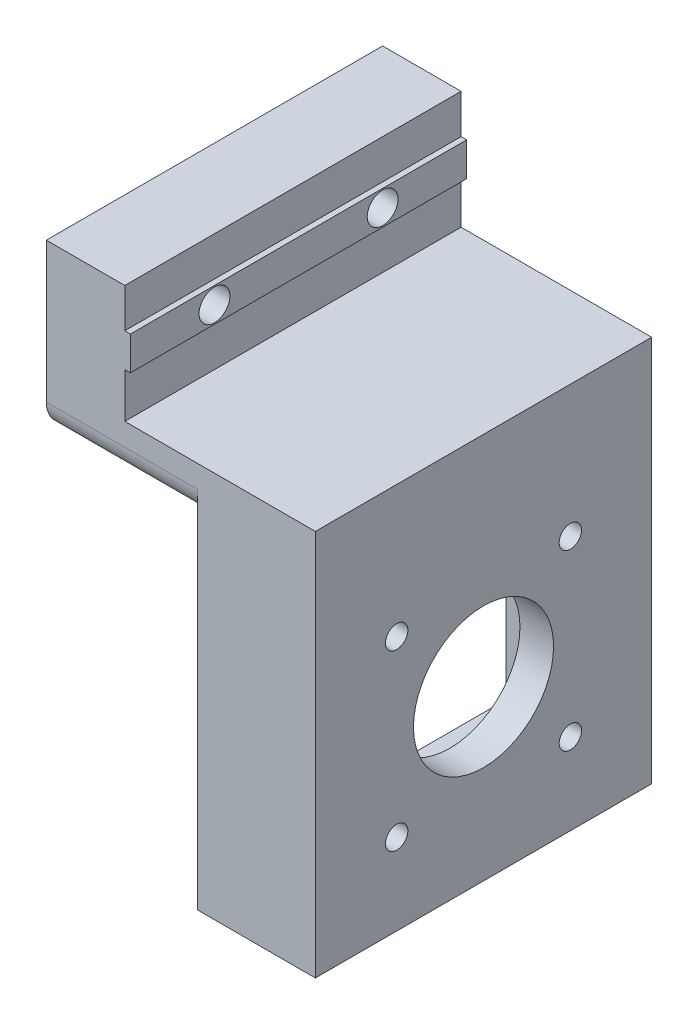
SolidWorks part; units mm, degrees
ref_plane "Alzado" through (0, 0, 0) normal (0, 0, 1) x (1, 0, 0)
ref_plane "Planta" through (0, 0, 0) normal (0, 1, 0) x (1, 0, 0)
ref_plane "Vista lateral" through (0, 0, 0) normal (1, 0, 0) x (0, 0, -1)
sketch "Croquis1" plane through (0, 0, 0) normal (0, 0, 1) x (1, 0, 0)
  line L0 (0, 0) -> (0, -30)
  line L1 (0, -30) -> (42, -30)
  line L2 (42, -30) -> (42, -90)
  line L3 (42, -90) -> (48, -90)
  line L4 (48, -90) -> (48, -21)
  line L5 (48, -21) -> (14, -21)
  line L6 (14, -21) -> (14, 0)
  line L7 (14, 0) -> (0, 0)
  dimension "D1" = 14
  dimension "D2" = 30
  dimension "D3" = 34
  dimension "D4" = 21
  dimension "D5" = 6
  dimension "D6" = 60
extrude "Saliente-Extruir1" add sketch "Croquis1" along normal blind 60
sketch "Croquis2" plane through (48, 0, 0) normal (1, 0, 0) x (0, 0, -1)
  line L0 (0, -90) -> (0, -21) construction
  line L1 (-45.5, -44.5) -> (-14.5, -44.5) construction
  line L2 (-45.5, -44.5) -> (-45.5, -75.5) construction
  line L3 (-45.5, -75.5) -> (-14.5, -75.5) construction
  line L4 (-14.5, -44.5) -> (-14.5, -75.5) construction
  line L5 (-60, -90) -> (0, -90) construction
  line L6 (-45.5, -44.5) -> (-14.5, -75.5) construction
  circle A0 centre (-45.5, -44.5) radius 2
  circle A1 centre (-14.5, -44.5) radius 2
  circle A2 centre (-45.5, -75.5) radius 2
  circle A3 centre (-14.5, -75.5) radius 2
  circle A4 centre (-30, -60) radius 12.5
  point P4 (-30, -75.5)
  point P7 (-45.5, -60)
  dimension "D5" = 4
  dimension "D6" = 4
  dimension "D7" = 4
  dimension "D8" = 4
  dimension "D9" = 25
  dimension "D1" = 31
  dimension "D2" = 31
  dimension "D3" = 30
  dimension "D4" = 30
extrude "Cortar-Extruir1" cut sketch "Croquis2" against normal up to next
sketch "Croquis3" plane through (42, 0, 0) normal (-1, 0, 0) x (0, 0, 1)
  line L0 (0, -30) -> (0, -90)
  line L1 (0, -90) -> (60, -90)
  line L2 (60, -90) -> (60, -30)
  line L3 (60, -30) -> (55, -30)
  line L4 (60, -30) -> (0, -30) construction
  line L5 (55, -30) -> (55, -85)
  line L6 (55, -85) -> (5, -85)
  line L7 (5, -85) -> (5, -30)
  line L8 (5, -30) -> (0, -30)
  dimension "D1" = 5
  dimension "D2" = 5
  dimension "D3" = 5
extrude "Saliente-Extruir2" add sketch "Croquis3" along normal blind 15
sketch "Croquis4" plane through (14, 0, 0) normal (1, 0, 0) x (0, 0, -1)
  line L0 (-60, -21) -> (-60, 0) construction
  line L1 (-60, -7) -> (0, -7)
  line L2 (-60, -7) -> (-60, -13)
  line L3 (-60, -13) -> (0, -13)
  line L4 (0, -7) -> (0, -13)
  line L5 (0, -21) -> (0, 0) construction
  line L6 (-60, 0) -> (0, 0) construction
  point P8 (-60, -10)
  dimension "D1" = 6
  dimension "D2" = 10
extrude "Saliente-Extruir3" add sketch "Croquis4" along normal blind 1
sketch "Croquis5" plane through (0, 0, 0) normal (-1, 0, 0) x (0, 0, 1)
  line L0 (60, 0) -> (0, 0) construction
  line L1 (0, 0) -> (0, -30) construction
  circle A0 centre (15, -10) radius 2.75
  circle A1 centre (45, -10) radius 2.75
  dimension "D5" = 5.5
  dimension "D6" = 5.5
  dimension "D1" = 10
  dimension "D2" = 10
  dimension "D3" = 30
  dimension "D4" = 15
extrude "Cortar-Extruir2" cut sketch "Croquis5" against normal up to next
sketch "Croquis6" plane through (0, 0, 0) normal (-1, 0, 0) x (0, 0, 1)
  circle A0 centre (15, -10) radius 6
  circle A1 centre (45, -10) radius 6
  dimension "D1" = 12
  dimension "D2" = 12
extrude "Cortar-Extruir3" cut sketch "Croquis6" against normal blind 8
fillet "Redondeo1" radius 5 2 edges at (13.5, -30, 60) (13.5, -30, 0)
